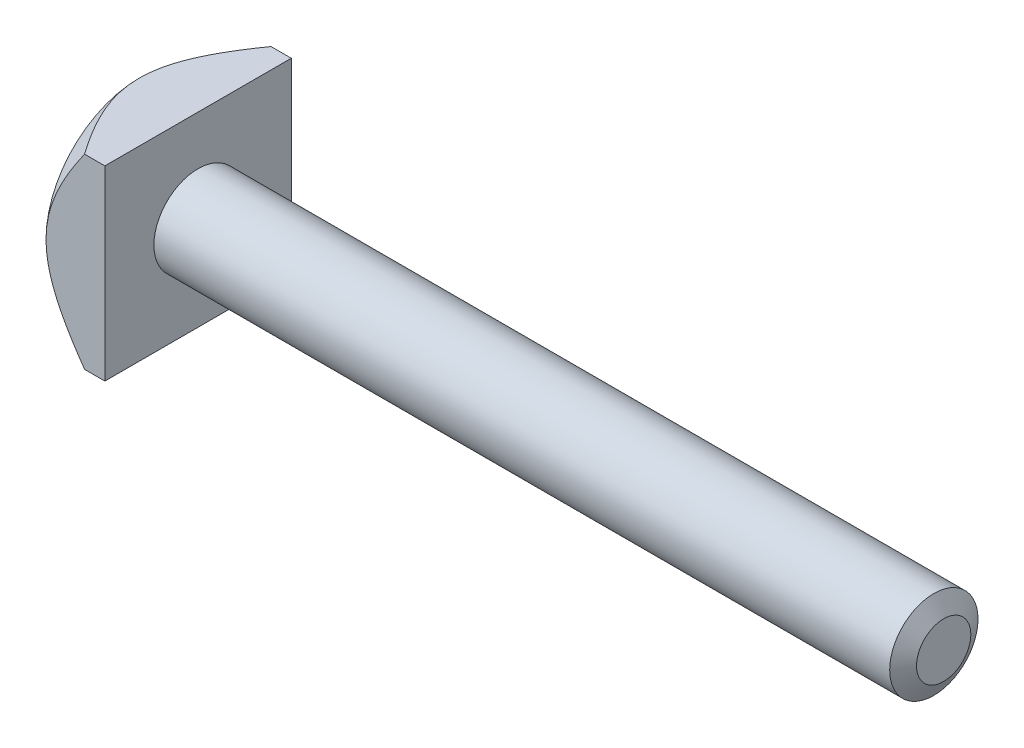
SolidWorks part; units mm, degrees
ref_plane "Front Plane" through (0, 0, 0) normal (0, 0, 1) x (1, 0, 0)
ref_plane "Top Plane" through (0, 0, 0) normal (0, 1, 0) x (1, 0, 0)
ref_plane "Right Plane" through (0, 0, 0) normal (1, 0, 0) x (0, 0, -1)
sketch "Sketch1" plane through (0, 0, 0) normal (1, 0, 0) x (0, 0, -1)
  line L1 (-9.5, -9.5) -> (9.5, -9.5)
  line L2 (-9.5, -9.5) -> (-9.5, 9.5)
  line L3 (-9.5, 9.5) -> (9.5, 9.5)
  line L4 (9.5, -9.5) -> (9.5, 9.5)
  line L5 (-9.5, -9.5) -> (9.5, 9.5) construction
  line L6 (-9.5, 9.5) -> (9.5, -9.5) construction
  point P0 (0, 0)
  dimension "D1" = 19
extrude "Boss-Extrude1" add sketch "Sketch1" along normal blind 6
sketch "Sketch2" plane through (6, 0, 0) normal (1, 0, 0) x (0, 0, -1)
  circle A0 centre (0, 0) radius 4.5
  dimension "D1" = 9
extrude "Boss-Extrude2" add sketch "Sketch2" along normal blind 76
chamfer "Chamfer1" distance 1 angle 60 1 edges at (82, 0, -4.5)
sketch "Sketch3" plane through (0, 0, 0) normal (-1, 0, 0) x (0, 0, 1)
  circle A0 centre (0, 0) radius 9.5
extrude "Cut-Extrude1" cut sketch "Sketch3" against normal blind 10 draft 45 flip side to cut
